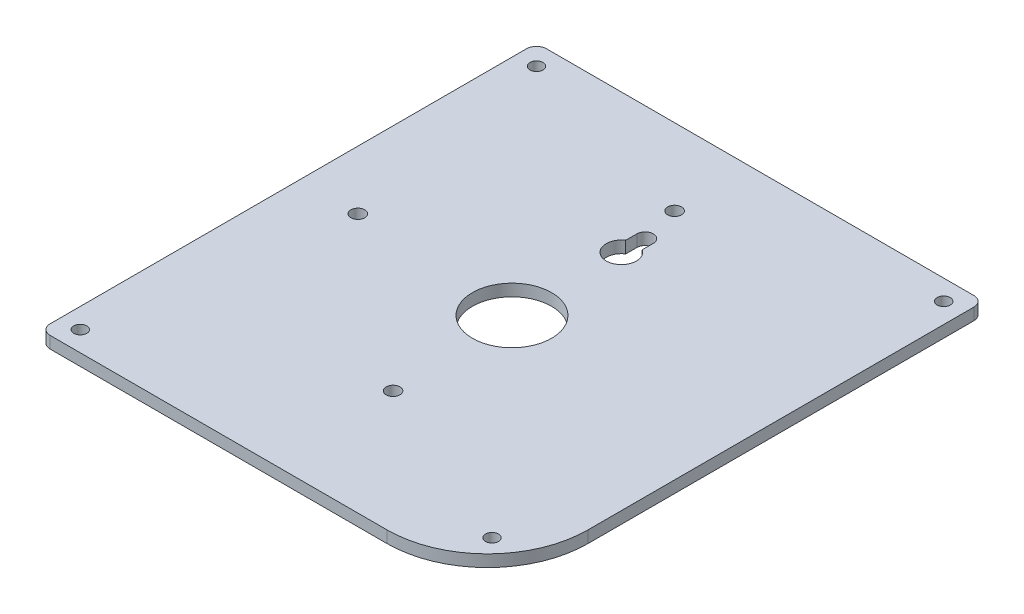
SolidWorks part; units mm, degrees
ref_plane "Front Plane" through (0, 0, 0) normal (0, 0, 1) x (1, 0, 0)
ref_plane "Top Plane" through (0, 0, 0) normal (0, 1, 0) x (1, 0, 0)
ref_plane "Right Plane" through (0, 0, 0) normal (1, 0, 0) x (0, 0, -1)
sketch "Sketch1" plane through (0, 0, 0) normal (0, 1, 0) x (1, 0, 0)
  line L0 (38.2045, 48.03) -> (-54.6555, 48.03) construction
  line L1 (-45.6855, 40.41) -> (29.2345, 40.41) construction
  line L2 (-45.6855, 40.41) -> (-45.6855, -59.5901) construction
  line L3 (-45.6855, -59.5901) -> (29.2345, -59.5901) construction
  line L4 (29.2345, 40.41) -> (29.2345, -59.5901) construction
  line L5 (48.2845, 53.11) -> (-64.7355, 53.11)
  line L6 (48.2845, 53.11) -> (48.2845, -46.8901)
  line L7 (22.8845, -72.2901) -> (-64.7355, -72.2901)
  line L8 (-64.7355, 53.11) -> (-64.7355, -72.2901)
  line L9 (-59.6555, 43.03) -> (-59.6555, -62.2101) construction
  line L10 (22.8845, -67.2101) -> (-54.6555, -67.2101) construction
  line L11 (43.2045, 43.03) -> (43.2045, -46.8901) construction
  line L12 (43.2045, 48.03) -> (-59.6555, 48.03) construction
  line L13 (-59.6555, 48.03) -> (-59.6555, -67.2101) construction
  line L14 (43.2045, 48.03) -> (43.2045, -46.8901) construction
  line L15 (22.8845, -67.2101) -> (-59.6555, -67.2101) construction
  line L16 (-54.6555, 48.03) -> (49945.3445, 48.03) construction
  line L17 (43.2045, 40.4991) -> (43.2045, -49959.5009) construction
  line L18 (-25.2243, -67.2101) -> (-50025.2243, -67.2101) construction
  line L19 (-59.6555, -48.2991) -> (-59.6555, -50048.2991) construction
  arc A0 (22.8845, -72.2901) -> (48.2845, -46.8901) centre (22.8845, -46.8901) ccw
  arc A1 (22.8845, -67.2101) -> (33.9996, -63.9006) centre (22.8845, -46.8901) ccw construction
  circle A2 centre (-59.6555, 48.03) radius 1.65
  arc A3 (-59.6555, 43.03) -> (-54.6555, 48.03) centre (-59.6555, 48.03) ccw construction
  arc A4 (38.2045, 48.03) -> (43.2045, 43.03) centre (43.2045, 48.03) ccw construction
  arc A5 (-54.6555, -67.2101) -> (-59.6555, -62.2101) centre (-59.6555, -67.2101) ccw construction
  arc A6 (40.7175, -56.631) -> (33.9996, -63.9006) centre (37.8809, -60.7485) ccw construction
  arc A7 (22.8845, -67.2101) -> (43.2045, -46.8901) centre (22.8845, -46.8901) ccw construction
  arc A8 (40.7175, -56.631) -> (43.2045, -46.8901) centre (22.8845, -46.8901) ccw construction
  circle A9 centre (43.2045, 48.03) radius 1.65
  circle A10 centre (-59.6555, -67.2101) radius 1.65
  circle A11 centre (37.8809, -60.7485) radius 1.65
  dimension "D3" = 50.8
  dimension "D7" = 25.4
  dimension "D8" = 25.4
  dimension "D9" = 5.08
  dimension "D10" = 3.3
  dimension "D11" = 10
  dimension "D12" = 3.3
  dimension "D13" = 5
  dimension "D14" = 5
  dimension "D15" = 3.3
  dimension "D16" = 3.3
  dimension "D17" = 5
  dimension "D1" = 100.0001
  dimension "D2" = 74.92
  dimension "0.75" = 19.05
  dimension "D4" = 19.05
  dimension "D5" = 12.7
  dimension "D6" = 12.7
extrude "Boss-Extrude3" add sketch "Sketch1" along normal blind 3
sketch "Sketch3" plane through (0, 3, 0) normal (0, 1, 0) x (1, 0, 0)
  line L0 (43.2045, 48.03) -> (-59.6555, 48.03) construction
  line L1 (-8.2255, 48.03) -> (-8.2255, 36.6926) construction
  line L2 (-35.978, 18.03) -> (49964.022, 18.03) construction
  line L3 (48.2845, 53.11) -> (-64.7355, 53.11) construction
  line L4 (-10.3083, 24.03) -> (-10.3083, 21.2203)
  line L5 (-6.1427, 24.03) -> (-6.1427, 21.2203)
  line L6 (-8.2255, 18.03) -> (-8.2255, -49951.97) construction
  line L22 (-59.6555, -67.2101) -> (22.8845, -67.2101)
  line L23 (43.2045, -46.8901) -> (43.2045, 48.03)
  line L24 (43.2045, 48.03) -> (-59.6555, 48.03)
  line L25 (-59.6555, 48.03) -> (-59.6555, -67.2101)
  line L26 (-59.6555, -67.2101) -> (22.8845, -67.2101) construction
  line L27 (43.2045, -46.8901) -> (43.2045, 48.03) construction
  line L28 (43.2045, 48.03) -> (-59.6555, 48.03) construction
  line L29 (-59.6555, 48.03) -> (-59.6555, -67.2101) construction
  arc A0 (-10.3083, 21.2203) -> (-6.1427, 21.2203) centre (-8.2255, 18.03) ccw
  arc A1 (-6.1427, 24.03) -> (-10.3083, 24.03) centre (-8.2255, 24.03) ccw
  arc A3 (22.8845, -67.2101) -> (43.2045, -46.8901) centre (22.8845, -46.8901) ccw
  arc A4 (22.8845, -67.2101) -> (43.2045, -46.8901) centre (22.8845, -46.8901) ccw construction
  point P6 (-8.2255, 48.03)
  dimension "D3" = 7.62
  dimension "D4" = 4.1656
  dimension "D1" = 30
  dimension "D5" = 6
  dimension "D6" = 35.08
  dimension "D2" = 5.08
extrude "Cut-Extrude1" cut sketch "Sketch3" against normal through all
sketch "Sketch4" plane through (0, 3, 0) normal (0, 1, 0) x (1, 0, 0)
  line L4 (48.2845, 53.11) -> (-64.7355, 53.11) construction
  line L5 (-53.7355, 41.11) -> (21.1845, 41.11) construction
  line L6 (-53.7355, 41.11) -> (-53.7355, -58.89) construction
  line L7 (-53.7355, -58.89) -> (21.1845, -58.89) construction
  line L8 (43.2045, -46.8901) -> (43.2045, 48.03)
  line L9 (-59.6555, -67.2101) -> (22.8845, -67.2101)
  line L10 (-59.6555, 48.03) -> (-59.6555, -67.2101)
  line L11 (43.2045, 48.03) -> (-59.6555, 48.03)
  line L12 (43.2045, -46.8901) -> (43.2045, 48.03) construction
  line L13 (-59.6555, -67.2101) -> (22.8845, -67.2101) construction
  line L14 (-59.6555, 48.03) -> (-59.6555, -67.2101) construction
  line L15 (43.2045, 48.03) -> (-59.6555, 48.03) construction
  line L16 (21.1845, 41.11) -> (21.1845, -58.89) construction
  line L17 (-64.7355, 53.11) -> (-64.7355, -72.2901) construction
  circle A1 centre (-49.9355, -6.82) radius 1.75
  arc A2 (22.8845, -67.2101) -> (43.2045, -46.8901) centre (22.8845, -46.8901) ccw
  arc A3 (22.8845, -67.2101) -> (43.2045, -46.8901) centre (22.8845, -46.8901) ccw construction
  circle A4 centre (-6.7555, -41.11) radius 1.75
  circle A5 centre (-10.5655, 33.82) radius 1.75
  dimension "D8" = 17.78
  dimension "D11" = 92.71
  dimension "D12" = 3.5
  dimension "D13" = 3.5
  dimension "D14" = 3.5
  dimension "D2" = 74.92
  dimension "D3" = 100
  dimension "D4" = 12
  dimension "D5" = 11
  dimension "D6" = 52.07
  dimension "D7" = 71.12
  dimension "D9" = 27.94
  dimension "D10" = 31.75
  dimension "D1" = 5.08
extrude "Cut-Extrude2" cut sketch "Sketch4" against normal through all
sketch "Sketch5" plane through (0, 3, 0) normal (0, 1, 0) x (1, 0, 0)
  line L1 (48.2845, 53.11) -> (-64.7355, 53.11) construction
  line L2 (-8.2255, 53.11) -> (-8.2255, -102.4216) construction
  line L3 (-64.7355, -9.59) -> (77.8378, -9.59) construction
  line L4 (-64.7355, 53.11) -> (-64.7355, -72.2901) construction
  circle A0 centre (-8.2255, -9.59) radius 10
  dimension "D1" = 20
extrude "Cut-Extrude3" cut sketch "Sketch5" against normal through all
fillet "Fillet1" radius 2.54 3 edges at (48.2845, 1.5, -53.11) (-64.7355, 1.5, -53.11) (-64.7355, 1.5, 72.2901)
